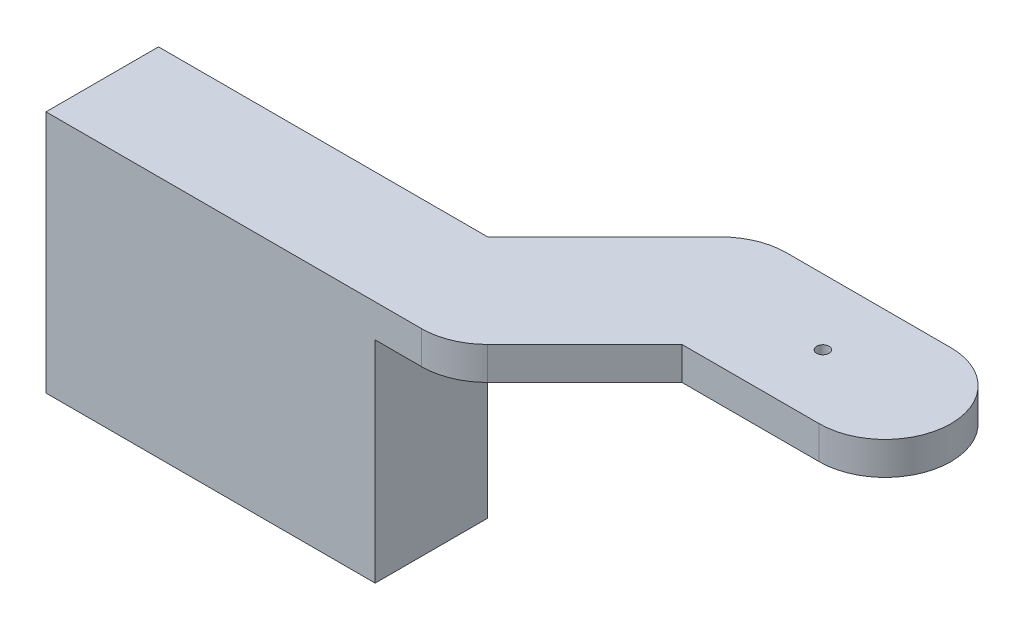
SolidWorks part; units mm, degrees
ref_plane "Plano frontal" through (0, 0, 0) normal (0, 0, 1) x (1, 0, 0)
ref_plane "Plano superior" through (0, 0, 0) normal (0, 1, 0) x (1, 0, 0)
ref_plane "Plano direito" through (0, 0, 0) normal (1, 0, 0) x (0, 0, -1)
sketch "Esboço1" plane through (0, 0, 0) normal (0, 1, 0) x (1, 0, 0)
  line L0 (-12.5, 0) -> (12.5, 0) construction
  line L1 (-12.5, 10) -> (12.5, 10)
  line L2 (-12.5, -10) -> (12.5, -10)
  line L3 (-12.5, 0) -> (-19.5711, 7.0711) construction
  line L4 (-19.5711, 7.0711) -> (-37.2487, -10.6066)
  line L5 (-37.2487, -10.6066) -> (-23.1066, -24.7487) construction
  line L6 (-23.1066, -24.7487) -> (-8.3579, -10)
  line L7 (-12.5, 0) -> (-8.3579, -10) construction
  line L8 (-30.1966, -27.6966) -> (-87.2487, -27.6966)
  line L9 (-87.2487, -10.6066) -> (-37.2487, -10.6066)
  line L10 (-87.2487, -10.6066) -> (-87.2487, -27.6966)
  line L11 (-30.1966, -17.6966) -> (-30.1966, -27.6966) construction
  line L14 (-37.2487, -10.6066) -> (-37.2487, -27.6966) construction
  arc A0 (-12.5, 10) -> (-12.5, -10) centre (-12.5, 0) ccw
  arc A1 (12.5, -10) -> (12.5, 10) centre (12.5, 0) ccw
  arc A2 (-30.1966, -27.6966) -> (-23.1066, -24.7487) centre (-30.1966, -17.6966) ccw
  point P2 (0, 0)
  dimension "D1" = 10
  dimension "D7" = 10
  dimension "D2" = 25
  dimension "D3" = 45
  dimension "D4" = 20
  dimension "D5" = 25
  dimension "D6" = 90
  dimension "D8" = 17.09
  dimension "D9" = 50
extrude "Ressalto-extrusão1" add sketch "Esboço1" against normal blind 5
sketch "Esboço2" plane through (0, -5, 0) normal (0, -1, 0) x (1, 0, 0)
  line L1 (-87.2487, 27.6966) -> (-37.2487, 27.6966)
  line L2 (-87.2487, 27.6966) -> (-87.2487, 10.6066)
  line L3 (-87.2487, 10.6066) -> (-37.2487, 10.6066)
  line L4 (-37.2487, 27.6966) -> (-37.2487, 10.6066)
extrude "Ressalto-extrusão2" add sketch "Esboço2" along normal blind 32
sketch "Esboço3" plane through (0, 0, 0) normal (0, 1, 0) x (1, 0, 0)
  line L2 (-12.5, 10) -> (12.5, 10) construction
  arc A1 (12.5, -10) -> (12.5, 10) centre (12.5, 0) ccw construction
  circle A3 centre (3.05, 0) radius 0.94
  dimension "D1" = 9.45
  dimension "D7" = 1.88
  dimension "D3" = 10
extrude "Corte-extrusão1" cut sketch "Esboço3" against normal through all
sketch "Esboço6" plane through (0, -5, 0) normal (0, 1, 0) x (1, 0, 0)
  line L0 (-11, 0) -> (3.05, 0) construction
  line L1 (-11, 2) -> (0.8409, 2.65)
  line L2 (-11, -2) -> (0.8409, -2.65)
  line L3 (3.05, 6.9875) -> (3.05, -7.5859) construction
  line L4 (17.1, -2) -> (5.2591, -2.65)
  line L5 (17.1, 2) -> (5.2591, 2.65)
  arc A0 (0.8409, -2.65) -> (5.2591, -2.65) centre (3.05, 0) ccw
  arc A1 (-11, 2) -> (-11, -2) centre (-11, 0) ccw
  arc A2 (17.1, 2) -> (17.1, -2) centre (17.1, 0) cw
  arc A3 (5.2591, 2.65) -> (0.8409, 2.65) centre (3.05, 0) ccw
  dimension "D1" = 4
  dimension "D2" = 6.9
  dimension "D3" = 14.05
  dimension "D4" = 5.3
extrude "Corte-extrusão2" cut sketch "Esboço6" along normal blind 2
